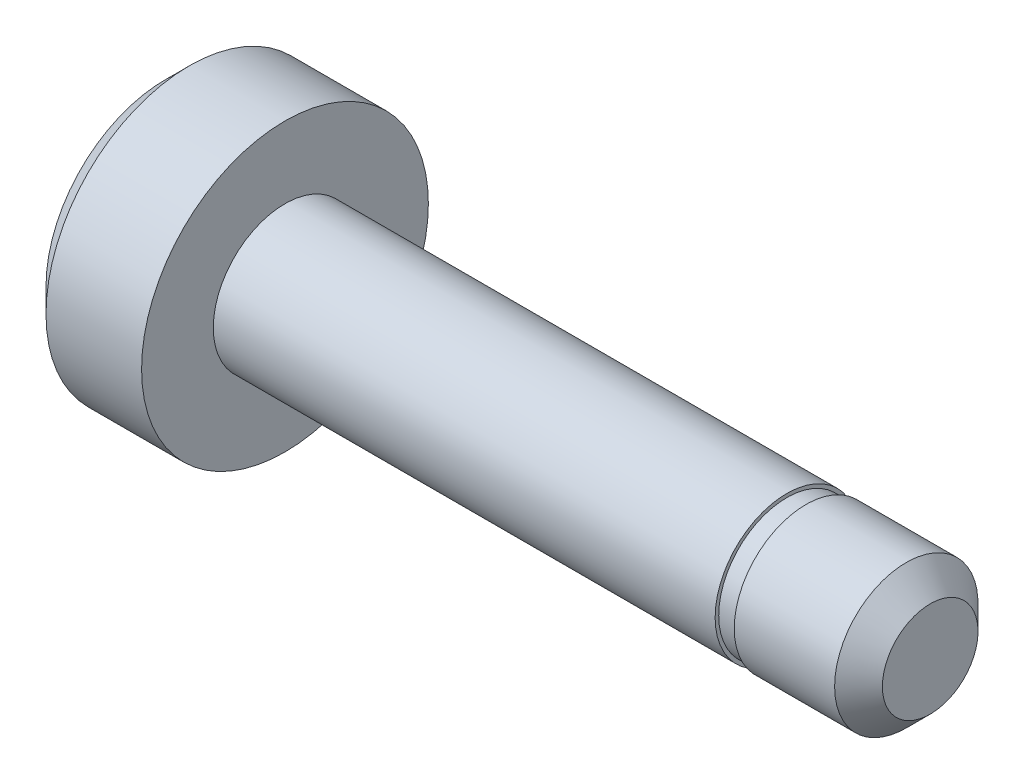
SolidWorks part; units mm, degrees
ref_plane "Plan de face" through (0, 0, 0) normal (0, 0, 1) x (1, 0, 0)
ref_plane "Plan de dessus" through (0, 0, 0) normal (0, 1, 0) x (1, 0, 0)
ref_plane "Plan de droite" through (0, 0, 0) normal (1, 0, 0) x (0, 0, -1)
sketch "Esquisse1" plane through (0, 0, 0) normal (0, 0, 1) x (1, 0, 0)
  line L0 (-27.0939, 0) -> (78.7283, 0) construction
  line L1 (0, 3) -> (0, 6)
  line L2 (0, 6) -> (-4, 6)
  line L3 (-5, 5) -> (-5, 0)
  line L4 (0, 3) -> (21, 3)
  line L5 (27, 2) -> (27, 0)
  line L6 (-4, 6) -> (-5, 5)
  line L7 (26, 3) -> (27, 2)
  line L8 (21.8, 3) -> (21.8, 2.85)
  line L9 (21.8, 2.85) -> (21, 2.85)
  line L10 (21, 2.85) -> (21, 3)
  line L11 (21.8, 3) -> (26, 3)
  line L12 (-5, 0) -> (27, 0)
  point P6 (-5, 6)
  point P8 (27, 3)
  dimension "D1" = 6
  dimension "D2" = 12
  dimension "D3" = 27
  dimension "D4" = 5
  dimension "D5" = 21
  dimension "D6" = 0.8
  dimension "D7" = 5.7
revolve "Révolution1" add sketch "Esquisse1" angle 360 about L0
